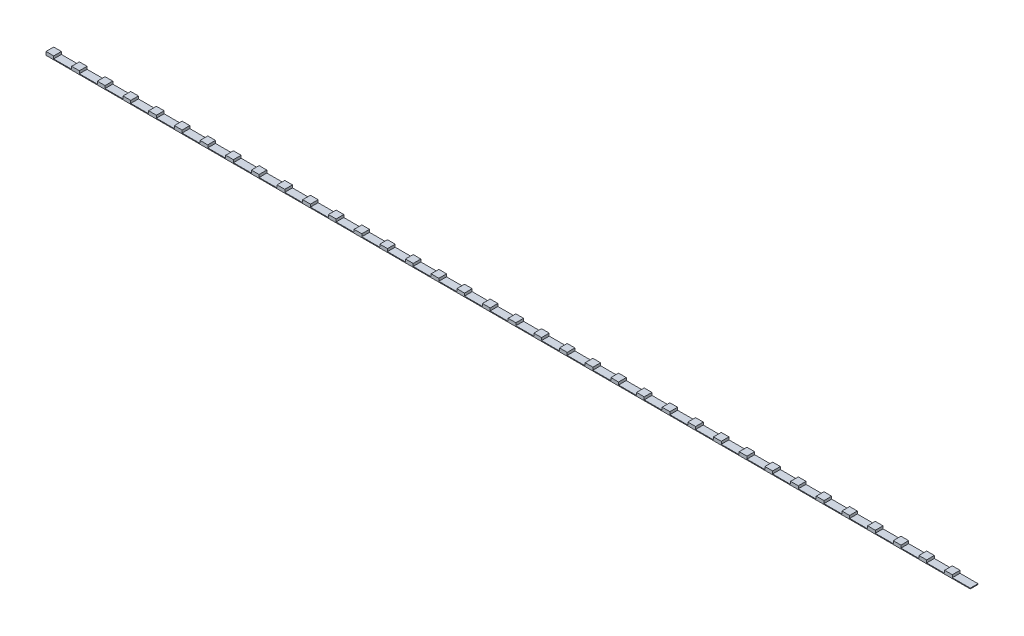
SolidWorks part; units mm, degrees
material "6061-T6 (SS)"
ref_plane "前视基准面" through (0, 0, 0) normal (0, 0, 1) x (1, 0, 0)
ref_plane "上视基准面" through (0, 0, 0) normal (0, 1, 0) x (1, 0, 0)
ref_plane "右视基准面" through (0, 0, 0) normal (1, 0, 0) x (0, 0, -1)
sketch "草图1" plane through (0, 0, 0) normal (0, 1, 0) x (1, 0, 0)
  line L1 (-300, 2.5) -> (300, 2.5)
  line L2 (-300, 2.5) -> (-300, -2.5)
  line L3 (-300, -2.5) -> (300, -2.5)
  line L4 (300, 2.5) -> (300, -2.5)
  line L5 (-300, 2.5) -> (300, -2.5) construction
  line L6 (-300, -2.5) -> (300, 2.5) construction
  point P0 (0, 0)
  dimension "D1" = 5
  dimension "D2" = 600
extrude "凸台-拉伸1" add sketch "草图1" along normal blind 0.5
sketch "草图2" plane through (0, 0.5, 0) normal (0, 1, 0) x (1, 0, 0)
  line L0 (300, 2.5) -> (-300, 2.5) construction
  line L1 (-300, -2.5) -> (-295, -2.5)
  line L2 (-300, -2.5) -> (-300, 2.5)
  line L3 (-300, 2.5) -> (-295, 2.5)
  line L4 (-295, -2.5) -> (-295, 2.5)
  dimension "D1" = 5
extrude "凸台-拉伸2" add sketch "草图2" along normal blind 1.7
pattern_linear "阵列(线性)1" count 36 spacing 16.6667 along (1, 0, 0) of "凸台-拉伸2"
